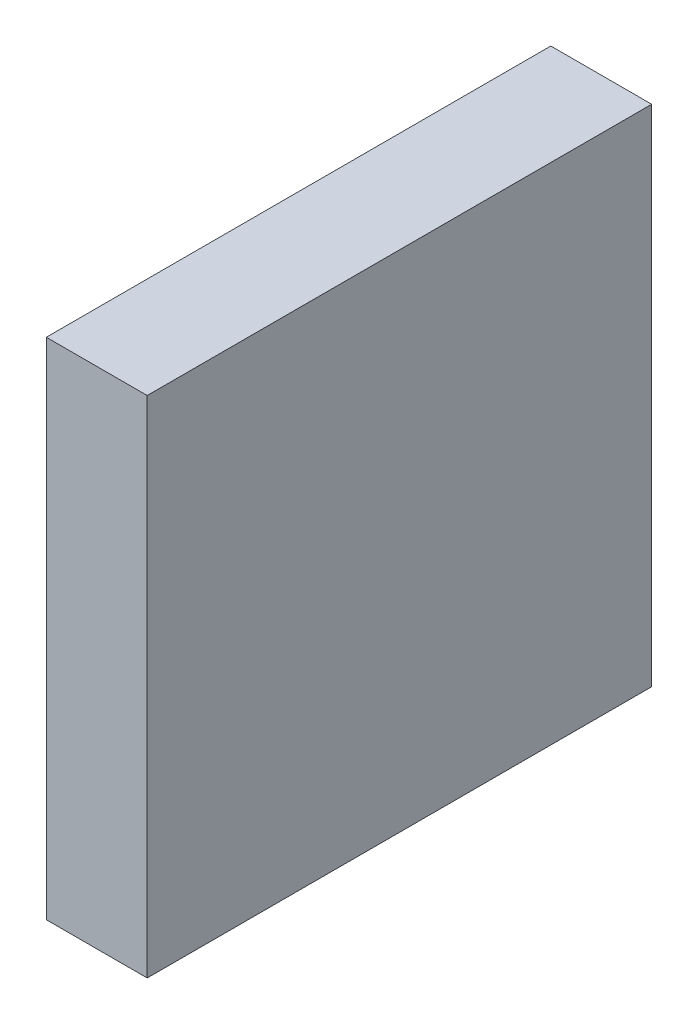
SolidWorks part; units mm, degrees
ref_plane "Płaszczyzna przednia" through (0, 0, 0) normal (0, 0, 1) x (1, 0, 0)
ref_plane "Płaszczyzna górna" through (0, 0, 0) normal (0, 1, 0) x (1, 0, 0)
ref_plane "Płaszczyzna prawa" through (0, 0, 0) normal (1, 0, 0) x (0, 0, -1)
sketch "Szkic1" plane through (0, 0, 0) normal (0, 0, 1) x (1, 0, 0)
  line L1 (-28.0311, 60.2514) -> (-16.0311, 60.2514)
  line L2 (-28.0311, 60.2514) -> (-28.0311, 0.2514)
  line L3 (-28.0311, 0.2514) -> (-16.0311, 0.2514)
  line L4 (-16.0311, 60.2514) -> (-16.0311, 0.2514)
  line L5 (-28.0311, 60.2514) -> (-16.0311, 0.2514) construction
  line L6 (-28.0311, 0.2514) -> (-16.0311, 60.2514) construction
  point P0 (-22.0311, 30.2514)
  dimension "D1" = 12
  dimension "D2" = 60
extrude "Dodanie-wyciągnięcie1" add sketch "Szkic1" along normal blind 60
